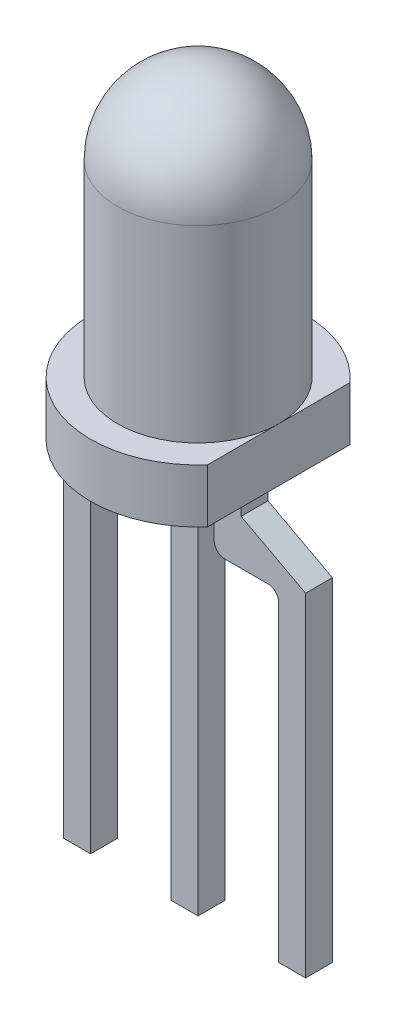
SolidWorks part; units mm, degrees
ref_plane "Plano frontal" through (0, 0, 0) normal (0, 0, 1) x (1, 0, 0)
ref_plane "Plano superior" through (0, 0, 0) normal (0, 1, 0) x (1, 0, 0)
ref_plane "Plano direito" through (0, 0, 0) normal (1, 0, 0) x (0, 0, -1)
sketch "Esboço1" plane through (0, 0, 0) normal (0, 1, 0) x (1, 0, 0)
  line L0 (0, -0.25) -> (0, 0.25) construction
  line L1 (-0.25, 0.25) -> (0.25, 0.25)
  line L2 (-0.25, 0.25) -> (-0.25, -0.25)
  line L3 (-0.25, -0.25) -> (0.25, -0.25)
  line L4 (0.25, 0.25) -> (0.25, -0.25)
  line L5 (-0.25, 0.25) -> (0.25, -0.25) construction
  line L6 (-0.25, -0.25) -> (0.25, 0.25) construction
  line L7 (1.75, 0.25) -> (2.25, 0.25)
  line L8 (1.75, 0.25) -> (1.75, -0.25)
  line L9 (1.75, -0.25) -> (2.25, -0.25)
  line L10 (2.25, 0.25) -> (2.25, -0.25)
  line L11 (1.75, 0.25) -> (2.25, -0.25) construction
  line L12 (1.75, -0.25) -> (2.25, 0.25) construction
  line L13 (-1.75, -0.25) -> (-2.25, 0.25) construction
  line L14 (-1.75, 0.25) -> (-2.25, -0.25) construction
  line L15 (-2.25, 0.25) -> (-2.25, -0.25)
  line L16 (-1.75, -0.25) -> (-2.25, -0.25)
  line L17 (-1.75, 0.25) -> (-1.75, -0.25)
  line L18 (-1.75, 0.25) -> (-2.25, 0.25)
  point P0 (0, 0)
  point P6 (2, 0)
  point P17 (-2, 0)
  dimension "D1" = 0.5
  dimension "D2" = 0.5
  dimension "D3" = 2
  dimension "D4" = 0.5
extrude "Ressalto-extrusão1" add sketch "Esboço1" along normal blind 1 and the other way blind 4
sketch "Esboço2" plane through (0, 0, 0.25) normal (0, 0, 1) x (1, 0, 0)
  line L0 (2.25, 1) -> (1.75, 1) construction
  line L1 (1.75, 1) -> (2.25, 1) construction
  line L2 (0, 1) -> (0, 3.9557) construction
  line L3 (-0.25, 1) -> (0.25, 1) construction
  line L4 (-2.25, 2.2) -> (-2.25, 1)
  line L5 (-1.05, 2.8387) -> (-2.25, 2.2)
  line L6 (-1.05, 3.43) -> (-1.05, 2.8387)
  line L7 (-0.55, 3.43) -> (-1.05, 3.43)
  line L8 (-0.25, 1) -> (-0.25, 3.43)
  line L9 (-0.25, 3.43) -> (0.25, 3.43)
  line L10 (0.25, 3.43) -> (0.25, 1)
  line L11 (1.75, 1) -> (1.75, 1.8)
  line L12 (1.55, 2) -> (0.75, 2)
  line L13 (0.55, 2.2) -> (0.55, 3.43)
  line L14 (0.55, 3.43) -> (1.05, 3.43)
  line L15 (1.05, 3.43) -> (1.05, 2.8387)
  line L16 (1.05, 2.8387) -> (2.25, 2.2)
  line L17 (2.25, 2.2) -> (2.25, 1)
  line L18 (-0.55, 2.4793) -> (-0.55, 3.43)
  line L19 (-1.55, 2) -> (-0.8677, 2)
  line L20 (-1.75, 1) -> (-1.75, 1.8)
  line L21 (-0.55, 2.4793) -> (-0.6677, 2.3769)
  line L22 (-0.6677, 2.3769) -> (-0.6677, 2.2)
  line L23 (0.8, 3.43) -> (0.8, 2.4793) construction
  line L24 (-2.25, 1) -> (-1.75, 1)
  line L25 (-0.25, 1) -> (0.25, 1)
  line L26 (1.75, 1) -> (2.25, 1)
  arc A0 (0.75, 2) -> (0.55, 2.2) centre (0.75, 2.2) cw
  arc A1 (1.75, 1.8) -> (1.55, 2) centre (1.55, 1.8) ccw
  arc A2 (-1.55, 2) -> (-1.75, 1.8) centre (-1.55, 1.8) ccw
  arc A3 (-0.6677, 2.2) -> (-0.8677, 2) centre (-0.8677, 2.2) cw
  point P0 (2, 1)
  point P36 (0.55, 2)
  point P39 (1.75, 2)
  point P44 (-1.75, 2)
  dimension "D5" = 0.2
  dimension "D6" = 0.2
  dimension "D1" = 0.5
  dimension "D2" = 0.5
  dimension "D3" = 2.43
  dimension "D4" = 1
  dimension "D7" = 0.8
extrude "Ressalto-extrusão2" add sketch "Esboço2" against normal up to surface (0.5 mm away) up to face at (0, -1.5, -0.25)
sketch "Esboço3" plane through (0, 3.43, 0) normal (0, 1, 0) x (1, 0, 0)
  line L0 (1.5, 1.3229) -> (1.5, -1.3229)
  arc A0 (1.5, 1.3229) -> (1.5, -1.3229) centre (0, 0) ccw
  dimension "D1" = 4
extrude "Ressalto-extrusão3" add sketch "Esboço3" along normal blind 1
sketch "Esboço4" plane through (0, 0, 0) normal (0, 0, 1) x (1, 0, 0)
  line L0 (0, 4.43) -> (0, 9.2259) construction
  line L1 (1.5, 4.43) -> (-2, 4.43) construction
  line L2 (0, 4.43) -> (1.5, 4.43)
  line L3 (1.5, 4.43) -> (1.5, 7.93)
  line L4 (0, 9.43) -> (0, 4.43)
  arc A0 (1.5, 7.93) -> (0, 9.43) centre (0, 7.93) ccw
  dimension "D1" = 1.5
  dimension "D2" = 5
revolve "Revolução1" add sketch "Esboço4" angle 360 about L0
